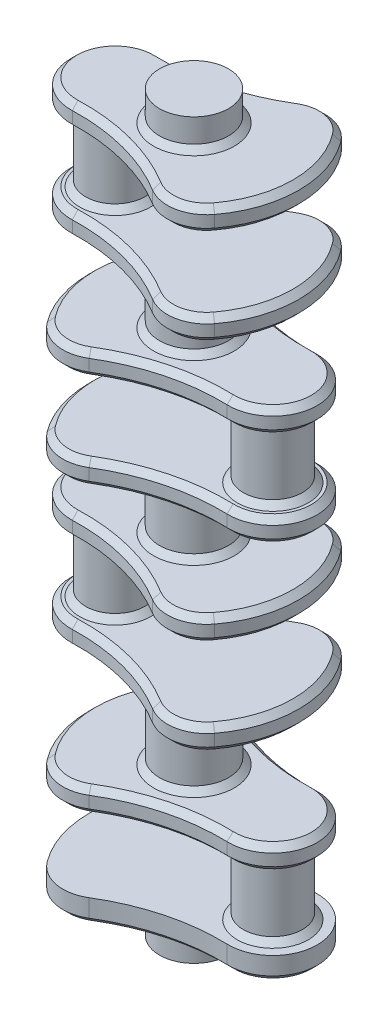
SolidWorks part; units mm, degrees
ref_plane "Alzado" through (0, 0, 0) normal (0, 0, 1) x (1, 0, 0)
ref_plane "Planta" through (0, 0, 0) normal (0, 1, 0) x (1, 0, 0)
ref_plane "Vista lateral" through (0, 0, 0) normal (1, 0, 0) x (0, 0, -1)
sketch "Croquis2" plane through (0, 0, 0) normal (0, 1, 0) x (1, 0, 0)
  line L0 (-84.4169, 0) -> (84.4169, 0) construction
  arc A0 (-16.0822, 37.0725) -> (-42.4638, 32.0481) centre (-26.5, 20) ccw
  arc A1 (39.2665, -22.488) -> (39.2665, 22.488) centre (40, 0) ccw
  arc A2 (-16.0822, 37.0725) -> (39.2665, 22.488) centre (36.0067, 122.4349) ccw
  arc A3 (-42.4638, 32.0481) -> (-42.4638, -32.0481) centre (0, 0) ccw
  arc A4 (-16.0822, -37.0725) -> (39.2665, -22.488) centre (36.0067, -122.4349) cw
  arc A5 (-16.0822, -37.0725) -> (-42.4638, -32.0481) centre (-26.5, -20) cw
  dimension "D2" = 40
  dimension "D3" = 45
  dimension "D5" = 200
  dimension "D1" = 26.5
  dimension "D4" = 40
extrude "Saliente-Extruir1" add sketch "Croquis2" along normal blind 12
sketch "Croquis3" plane through (0, 0, 0) normal (0, -1, 0) x (1, 0, 0)
  circle A0 centre (0, 0) radius 17.5
  dimension "D1" = 35
extrude "Saliente-Extruir2" add sketch "Croquis3" along normal blind 15
ref_plane "Plano1" through (0, 48, 0) normal (0, 1, 0) x (1, 0, 0)
sketch "Croquis4" plane through (0, 48, 0) normal (0, 1, 0) x (1, 0, 0)
  arc A0 (-16.0822, 37.0725) -> (-42.4638, 32.0481) centre (-26.5, 20) ccw construction
  arc A1 (-42.4638, 32.0481) -> (-42.4638, -32.0481) centre (0, 0) ccw construction
  arc A2 (-42.4638, -32.0481) -> (-16.0822, -37.0725) centre (-26.5, -20) ccw construction
  arc A3 (39.2665, -22.488) -> (-16.0822, -37.0725) centre (36.0067, -122.4349) ccw construction
  arc A4 (39.2665, -22.488) -> (39.2665, 22.488) centre (40, 0) ccw construction
  arc A5 (-16.0822, 37.0725) -> (39.2665, 22.488) centre (36.0067, 122.4349) ccw construction
  arc A6 (-16.0822, 37.0725) -> (-42.4638, 32.0481) centre (-26.5, 20) ccw
  arc A7 (-42.4638, 32.0481) -> (-42.4638, -32.0481) centre (0, 0) ccw
  arc A8 (-42.4638, -32.0481) -> (-16.0822, -37.0725) centre (-26.5, -20) ccw
  arc A9 (39.2665, -22.488) -> (-16.0822, -37.0725) centre (36.0067, -122.4349) ccw
  arc A10 (39.2665, -22.488) -> (39.2665, 22.488) centre (40, 0) ccw
  arc A11 (-16.0822, 37.0725) -> (39.2665, 22.488) centre (36.0067, 122.4349) ccw
extrude "Saliente-Extruir3" add sketch "Croquis4" along normal blind 12 separate body
sketch "Croquis6" plane through (0, 48, 0) normal (0, -1, 0) x (-1, 0, 0)
  arc A0 (-39.2665, 22.488) -> (-39.2665, -22.488) centre (-40, 0) ccw construction
  arc A1 (-39.2665, 22.488) -> (-39.2665, -22.488) centre (-40, 0) ccw
  circle A2 centre (-40, 0) radius 15
  point P4 (23.297, -3.5018)
  dimension "D1" = 30
sketch "Croquis7" plane through (0, 0, 0) normal (0, -1, 0) x (-1, 0, 0)
extrude "Saliente-Extruir4" add sketch "Croquis6" along normal up to next (36 mm away) contours A2
ref_plane "Plano2" through (0, 102, 0) normal (0, 1, 0) x (1, 0, 0)
sketch "Croquis8" plane through (0, 102, 0) normal (0, 1, 0) x (1, 0, 0)
  arc A6 (-39.2665, 22.488) -> (-39.2665, -22.488) centre (-40, 0) ccw
  arc A7 (-39.2665, 22.488) -> (16.0822, 37.0725) centre (-36.0067, 122.4349) ccw
  arc A8 (16.0822, -37.0725) -> (-39.2665, -22.488) centre (-36.0067, -122.4349) ccw
  arc A9 (16.0822, -37.0725) -> (42.4638, -32.0481) centre (26.5, -20) ccw
  arc A10 (42.4638, -32.0481) -> (42.4638, 32.0481) centre (0, 0) ccw
  arc A11 (42.4638, 32.0481) -> (16.0822, 37.0725) centre (26.5, 20) ccw
  dimension "D1" = 22.5
  dimension "D2" = 100
  dimension "D3" = 20
  dimension "D4" = 53.2002
  dimension "D5" = 16.0822
  dimension "D6" = 26.5
extrude "Saliente-Extruir6" add sketch "Croquis8" along normal blind 12 separate body
sketch "Croquis9" plane through (0, 102, 0) normal (0, -1, 0) x (1, 0, 0)
  circle A0 centre (0, 0) radius 17.5 construction
  circle A1 centre (0, 0) radius 17.5
extrude "Saliente-Extruir7" add sketch "Croquis9" along normal up to next (42 mm away)
ref_plane "Plano3" through (0, 150, 0) normal (0, -1, 0) x (-1, 0, 0)
sketch "Croquis10" plane through (0, 150, 0) normal (0, -1, 0) x (-1, 0, 0)
  arc A0 (-42.4638, 32.0481) -> (-42.4638, -32.0481) centre (0, 0) ccw construction
  arc A1 (-42.4638, -32.0481) -> (-16.0822, -37.0725) centre (-26.5, -20) ccw construction
  arc A2 (-16.0822, 37.0725) -> (-42.4638, 32.0481) centre (-26.5, 20) ccw construction
  arc A3 (-16.0822, 37.0725) -> (39.2665, 22.488) centre (36.0067, 122.4349) ccw construction
  arc A4 (39.2665, -22.488) -> (39.2665, 22.488) centre (40, 0) ccw construction
  arc A5 (39.2665, -22.488) -> (-16.0822, -37.0725) centre (36.0067, -122.4349) ccw construction
  arc A6 (-42.4638, 32.0481) -> (-42.4638, -32.0481) centre (0, 0) ccw
  arc A7 (-42.4638, -32.0481) -> (-16.0822, -37.0725) centre (-26.5, -20) ccw
  arc A8 (-16.0822, 37.0725) -> (-42.4638, 32.0481) centre (-26.5, 20) ccw
  arc A9 (-16.0822, 37.0725) -> (39.2665, 22.488) centre (36.0067, 122.4349) ccw
  arc A10 (39.2665, -22.488) -> (39.2665, 22.488) centre (40, 0) ccw
  arc A11 (39.2665, -22.488) -> (-16.0822, -37.0725) centre (36.0067, -122.4349) ccw
extrude "Saliente-Extruir8" add sketch "Croquis10" against normal blind 12 separate body
sketch "Croquis11" plane through (0, 150, 0) normal (0, -1, 0) x (1, 0, 0)
  circle A0 centre (-40, 0) radius 15
  dimension "D1" = 30
extrude "Saliente-Extruir10" add sketch "Croquis11" along normal up to next (36 mm away)
ref_plane "Plano4" through (0, 192, 0) normal (0, -1, 0) x (-1, 0, 0)
sketch "Croquis12" plane through (0, 192, 0) normal (0, -1, 0) x (-1, 0, 0)
  arc A6 (-39.2665, 22.488) -> (16.0822, 37.0725) centre (-36.0067, 122.4349) ccw
  arc A7 (42.4638, 32.0481) -> (16.0822, 37.0725) centre (26.5, 20) ccw
  arc A8 (42.4638, -32.0481) -> (42.4638, 32.0481) centre (0, 0) ccw
  arc A9 (16.0822, -37.0725) -> (42.4638, -32.0481) centre (26.5, -20) ccw
  arc A10 (16.0822, -37.0725) -> (-39.2665, -22.488) centre (-36.0067, -122.4349) ccw
  arc A11 (-39.2665, 22.488) -> (-39.2665, -22.488) centre (-40, 0) ccw
  arc A12 (-39.2665, 22.488) -> (16.0822, 37.0725) centre (-36.0067, 122.4349) ccw
  arc A13 (42.4638, 32.0481) -> (16.0822, 37.0725) centre (26.5, 20) ccw
  arc A14 (42.4638, -32.0481) -> (42.4638, 32.0481) centre (0, 0) ccw
  arc A15 (16.0822, -37.0725) -> (42.4638, -32.0481) centre (26.5, -20) ccw
  arc A16 (16.0822, -37.0725) -> (-39.2665, -22.488) centre (-36.0067, -122.4349) ccw
  arc A17 (-39.2665, 22.488) -> (-39.2665, -22.488) centre (-40, 0) ccw
  dimension "D1" = 0
extrude "Saliente-Extruir11" add sketch "Croquis12" against normal blind 12 separate body
sketch "Croquis13" plane through (0, 192, 0) normal (0, -1, 0) x (1, 0, 0)
  circle A0 centre (0, 0) radius 17.5 construction
  circle A1 centre (0, 0) radius 17.5
extrude "Saliente-Extruir12" add sketch "Croquis13" along normal up to next (30 mm away)
ref_plane "Plano5" through (0, 240, 0) normal (0, -1, 0) x (-1, 0, 0)
sketch "Croquis14" plane through (0, 240, 0) normal (0, -1, 0) x (-1, 0, 0)
  arc A6 (-39.2665, 22.488) -> (-39.2665, -22.488) centre (-40, 0) ccw
  arc A7 (-39.2665, 22.488) -> (16.0822, 37.0725) centre (-36.0067, 122.4349) ccw
  arc A8 (42.4638, 32.0481) -> (16.0822, 37.0725) centre (26.5, 20) ccw
  arc A9 (42.4638, -32.0481) -> (42.4638, 32.0481) centre (0, 0) ccw
  arc A10 (16.0822, -37.0725) -> (42.4638, -32.0481) centre (26.5, -20) ccw
  arc A11 (16.0822, -37.0725) -> (-39.2665, -22.488) centre (-36.0067, -122.4349) ccw
  arc A12 (-39.2665, 22.488) -> (-39.2665, -22.488) centre (-40, 0) ccw
  arc A13 (-39.2665, 22.488) -> (16.0822, 37.0725) centre (-36.0067, 122.4349) ccw
  arc A14 (42.4638, 32.0481) -> (16.0822, 37.0725) centre (26.5, 20) ccw
  arc A15 (42.4638, -32.0481) -> (42.4638, 32.0481) centre (0, 0) ccw
  arc A16 (16.0822, -37.0725) -> (42.4638, -32.0481) centre (26.5, -20) ccw
  arc A17 (16.0822, -37.0725) -> (-39.2665, -22.488) centre (-36.0067, -122.4349) ccw
  dimension "D1" = 0
extrude "Saliente-Extruir13" add sketch "Croquis14" against normal blind 12 separate body
sketch "Croquis15" plane through (0, 240, 0) normal (0, -1, 0) x (1, 0, 0)
  circle A0 centre (40, 0) radius 15
  dimension "D1" = 30
extrude "Saliente-Extruir14" add sketch "Croquis15" along normal up to next (36 mm away)
ref_plane "Plano6" through (0, 282, 0) normal (0, -1, 0) x (-1, 0, 0)
sketch "Croquis17" plane through (0, 282, 0) normal (0, -1, 0) x (-1, 0, 0)
  arc A6 (-16.0822, 37.0725) -> (-42.4638, 32.0481) centre (-26.5, 20) ccw
  arc A7 (-16.0822, 37.0725) -> (39.2665, 22.488) centre (36.0067, 122.4349) ccw
  arc A8 (39.2665, -22.488) -> (39.2665, 22.488) centre (40, 0) ccw
  arc A9 (39.2665, -22.488) -> (-16.0822, -37.0725) centre (36.0067, -122.4349) ccw
  arc A10 (-42.4638, -32.0481) -> (-16.0822, -37.0725) centre (-26.5, -20) ccw
  arc A11 (-42.4638, 32.0481) -> (-42.4638, -32.0481) centre (0, 0) ccw
  arc A12 (-16.0822, 37.0725) -> (-42.4638, 32.0481) centre (-26.5, 20) ccw
  arc A13 (-16.0822, 37.0725) -> (39.2665, 22.488) centre (36.0067, 122.4349) ccw
  arc A14 (39.2665, -22.488) -> (39.2665, 22.488) centre (40, 0) ccw
  arc A15 (39.2665, -22.488) -> (-16.0822, -37.0725) centre (36.0067, -122.4349) ccw
  arc A16 (-42.4638, -32.0481) -> (-16.0822, -37.0725) centre (-26.5, -20) ccw
  arc A17 (-42.4638, 32.0481) -> (-42.4638, -32.0481) centre (0, 0) ccw
  dimension "D1" = 0
extrude "Saliente-Extruir16" add sketch "Croquis17" against normal blind 12 separate body
sketch "Croquis18" plane through (0, 282, 0) normal (0, -1, 0) x (1, 0, 0)
  circle A0 centre (0, 0) radius 17.5 construction
  circle A1 centre (0, 0) radius 17.5
extrude "Saliente-Extruir17" add sketch "Croquis18" along normal up to next (30 mm away)
ref_plane "Plano7" through (0, 330, 0) normal (0, -1, 0) x (-1, 0, 0)
sketch "Croquis19" plane through (0, 330, 0) normal (0, -1, 0) x (-1, 0, 0)
  arc A6 (-16.0822, 37.0725) -> (39.2665, 22.488) centre (36.0067, 122.4349) ccw
  arc A7 (39.2665, -22.488) -> (39.2665, 22.488) centre (40, 0) ccw
  arc A8 (39.2665, -22.488) -> (-16.0822, -37.0725) centre (36.0067, -122.4349) ccw
  arc A9 (-42.4638, -32.0481) -> (-16.0822, -37.0725) centre (-26.5, -20) ccw
  arc A10 (-42.4638, 32.0481) -> (-42.4638, -32.0481) centre (0, 0) ccw
  arc A11 (-16.0822, 37.0725) -> (-42.4638, 32.0481) centre (-26.5, 20) ccw
  arc A12 (-16.0822, 37.0725) -> (39.2665, 22.488) centre (36.0067, 122.4349) ccw
  arc A13 (39.2665, -22.488) -> (39.2665, 22.488) centre (40, 0) ccw
  arc A14 (39.2665, -22.488) -> (-16.0822, -37.0725) centre (36.0067, -122.4349) ccw
  arc A15 (-42.4638, -32.0481) -> (-16.0822, -37.0725) centre (-26.5, -20) ccw
  arc A16 (-42.4638, 32.0481) -> (-42.4638, -32.0481) centre (0, 0) ccw
  arc A17 (-16.0822, 37.0725) -> (-42.4638, 32.0481) centre (-26.5, 20) ccw
  dimension "D1" = 0
extrude "Saliente-Extruir18" add sketch "Croquis19" against normal blind 12 separate body
sketch "Croquis20" plane through (0, 330, 0) normal (0, -1, 0) x (1, 0, 0)
  circle A0 centre (-40, 0) radius 15 construction
  circle A1 centre (-40, 0) radius 15
extrude "Saliente-Extruir19" add sketch "Croquis20" along normal up to next (36 mm away)
sketch "Croquis21" plane through (0, 342, 0) normal (0, 1, 0) x (1, 0, 0)
  circle A0 centre (0, 0) radius 17.5 construction
  circle A1 centre (0, 0) radius 17.5
extrude "Saliente-Extruir20" add sketch "Croquis21" along normal blind 15
chamfer "Chaflán2" distance 3 angle 45 106 edges at (40, 12, 15) (0, 60, 17.5) (62.5, 60, 0) (10.5264, 60, 25.7356) (-30.2417, 60, 39.6469) (-53.2002, 60, 0) (-30.2417, 60, -39.6469) (10.5264, 60, -25.7356) (40, 240, -15) (-30.2417, 240, -39.6469) (-53.2002, 240, 0) (-30.2417, 240, 39.6469) (10.5264, 240, 25.7356) (62.5, 240, 0) (10.5264, 240, -25.7356) (0, 192, -17.5) (10.5264, 192, -25.7356) (-30.2417, 192, -39.6469) (-53.2002, 192, 0) (-30.2417, 192, 39.6469) (10.5264, 192, 25.7356) (62.5, 192, 0) (-40, 150, -15) (-10.5264, 150, -25.7356) (-62.5, 150, 0) (-10.5264, 150, 25.7356) (30.2417, 150, 39.6469) (53.2002, 150, 0) (30.2417, 150, -39.6469) (0, 102, 17.5) (-62.5, 102, 0) (-10.5264, 102, 25.7356) (30.2417, 102, 39.6469) (53.2002, 102, 0) (30.2417, 102, -39.6469) (-10.5264, 102, -25.7356) (40, 48, 15) (-30.2417, 48, -39.6469) (-53.2002, 48, 0) (-30.2417, 48, 39.6469) (10.5264, 48, 25.7356) (62.5, 48, 0) (10.5264, 48, -25.7356) (0, 0, 17.5) (-30.2417, 0, 39.6469) (10.5264, 0, 25.7356) (62.5, 0, 0) (10.5264, 0, -25.7356) (-30.2417, 0, -39.6469) (-53.2002, 0, 0) (-40, 114, 15) (30.2417, 114, -39.6469) (53.2002, 114, 0) (30.2417, 114, 39.6469) (-10.5264, 114, 25.7356) (-62.5, 114, 0) (-10.5264, 114, -25.7356) (0, 162, -17.5) (53.2002, 162, 0) (30.2417, 162, 39.6469) (-10.5264, 162, 25.7356) (-62.5, 162, 0) (-10.5264, 162, -25.7356) (30.2417, 162, -39.6469) (40, 204, -15) (10.5264, 204, 25.7356) (-30.2417, 204, 39.6469) (-53.2002, 204, 0) (-30.2417, 204, -39.6469) (10.5264, 204, -25.7356) (62.5, 204, 0) (0, 252, -17.5) (62.5, 252, 0) (10.5264, 252, 25.7356) (-30.2417, 252, 39.6469) (-53.2002, 252, 0) (-30.2417, 252, -39.6469) (10.5264, 252, -25.7356) (0, 282, -17.5) (-62.5, 282, 0) (-10.5264, 282, 25.7356) (30.2417, 282, 39.6469) (53.2002, 282, 0) (30.2417, 282, -39.6469) (-10.5264, 282, -25.7356) (-40, 294, -15) (30.2417, 294, -39.6469) (53.2002, 294, 0) (30.2417, 294, 39.6469) (-10.5264, 294, 25.7356) (-62.5, 294, 0) (-10.5264, 294, -25.7356) (-40, 330, -15) (-10.5264, 330, -25.7356) (-62.5, 330, 0) (-10.5264, 330, 25.7356) (30.2417, 330, 39.6469) (53.2002, 330, 0) (30.2417, 330, -39.6469) (0, 342, -17.5) (53.2002, 342, 0) (30.2417, 342, 39.6469) (-10.5264, 342, 25.7356) (-62.5, 342, 0) (-10.5264, 342, -25.7356) (30.2417, 342, -39.6469)
